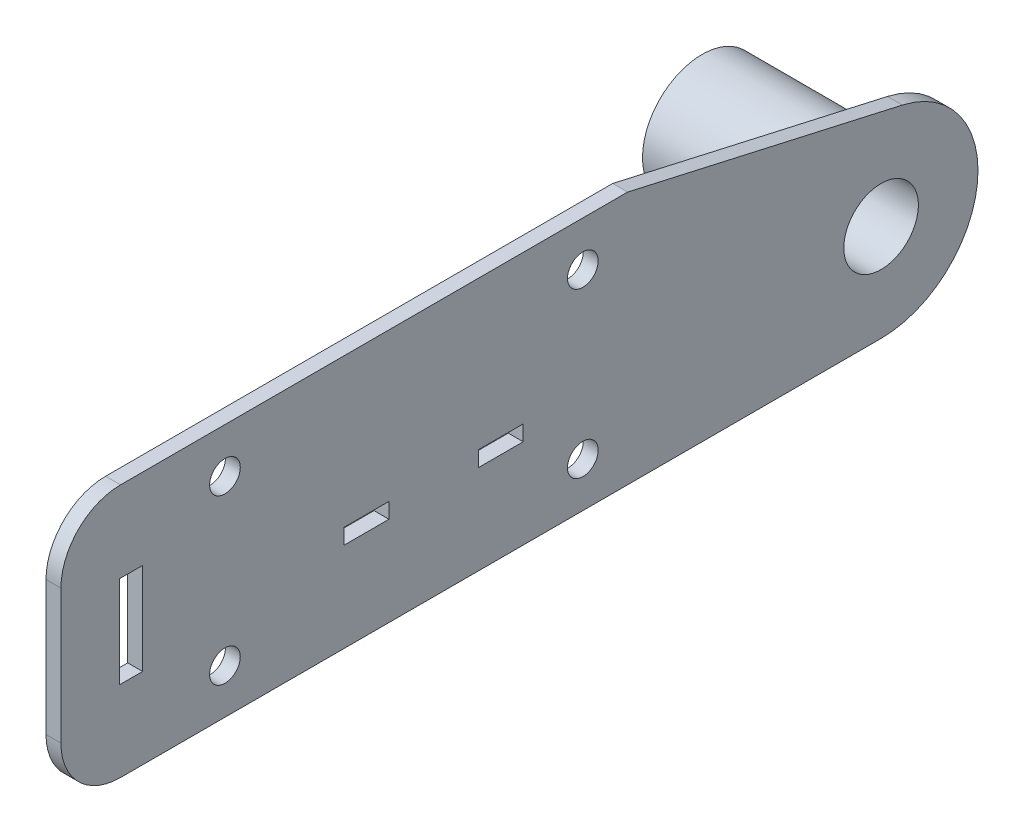
SolidWorks part; units mm, degrees
material "Plain Carbon Steel"
ref_plane "Front Plane" through (0, 0, 0) normal (0, 0, 1) x (1, 0, 0)
ref_plane "Top Plane" through (0, 0, 0) normal (0, 1, 0) x (1, 0, 0)
ref_plane "Right Plane" through (0, 0, 0) normal (1, 0, 0) x (0, 0, -1)
sketch "Sketch1" plane through (0, 0, 0) normal (1, 0, 0) x (0, 0, -1)
  line L0 (47.625, -26.9875) -> (101.6, -26.9875)
  line L1 (38.1, 17.4625) -> (-38.1, 17.4625)
  line L2 (38.1, 17.4625) -> (38.1, -17.4625)
  line L3 (38.1, -17.4625) -> (-38.1, -17.4625)
  line L4 (-38.1, 17.4625) -> (-38.1, -17.4625)
  line L5 (38.1, 17.4625) -> (-38.1, -17.4625) construction
  line L6 (38.1, -17.4625) -> (-38.1, 17.4625) construction
  line L7 (-47.625, 26.9875) -> (47.625, 26.9875)
  line L8 (-47.625, 26.9875) -> (-47.625, -26.9875)
  line L9 (-47.625, -26.9875) -> (47.625, -26.9875)
  line L10 (47.625, 26.9875) -> (47.625, -26.9875)
  line L11 (-47.625, 26.9875) -> (47.625, -26.9875) construction
  line L12 (-47.625, -26.9875) -> (47.625, 26.9875) construction
  line L13 (47.625, 26.9875) -> (106.1432, 13.7812)
  circle A0 centre (-38.1, 17.4625) radius 3.2639
  circle A1 centre (-38.1, -17.4625) radius 3.2639
  circle A2 centre (38.1, -17.4625) radius 3.2639
  circle A3 centre (38.1, 17.4625) radius 3.2639
  circle A4 centre (101.6, -6.35) radius 12.7
  circle A5 centre (101.6, -6.35) radius 20.6375
  point P0 (0, 0)
  point P13 (0, 0)
  dimension "D3" = 6.5278
  dimension "D4" = 25.4
  dimension "D1" = 76.2
  dimension "D2" = 34.925
  dimension "D5" = 63.5
  dimension "D6" = 6.35
  dimension "D8" = 9.525
  dimension "D9" = 9.525
extrude "Boss-Extrude1" add sketch "Sketch1" along normal blind 3.175 contours L10 L7 L8 L9 A3 L2 A2 L3 A1 L4 A0 L1 | A3 L1 A0 L4 A1 L3 A2 L2 | A5 L13 L10 L0 | A5 A4
sketch "Sketch2" plane through (0, 0, 0) normal (-1, 0, 0) x (0, 0, 1)
  circle A0 centre (-101.6, -6.35) radius 12.7 construction
  circle A1 centre (-101.6, -6.35) radius 12.7
  circle A2 centre (-101.6, -6.35) radius 7.9375
  dimension "D1" = 4.7625
extrude "Boss-Extrude2" add sketch "Sketch2" along normal blind 34.925 and the other way blind 3.175
sketch "Sketch4" plane through (3.175, 0, 0) normal (1, 0, 0) x (0, 0, -1)
  line L0 (-47.625, -26.9875) -> (101.6, -26.9875) construction
  line L1 (-47.625, 26.9875) -> (-60.325, 26.9875)
  line L2 (-47.625, 26.9875) -> (-47.625, -26.9875)
  line L3 (-47.625, -26.9875) -> (-60.325, -26.9875)
  line L4 (-73.025, 14.2875) -> (-73.025, -14.2875)
  line L6 (-60.579, 9.779) -> (-55.626, 9.779)
  line L7 (-60.579, 9.779) -> (-60.579, -9.779)
  line L8 (-60.579, -9.779) -> (-55.626, -9.779)
  line L9 (-55.626, 9.779) -> (-55.626, -9.779)
  arc A0 (-60.325, 26.9875) -> (-73.025, 14.2875) centre (-60.325, 14.2875) ccw
  arc A1 (-60.325, -26.9875) -> (-73.025, -14.2875) centre (-60.325, -14.2875) cw
  point P13 (-73.025, 26.9875)
  dimension "D6" = 12.7
  dimension "D1" = 25.4
  dimension "D2" = 19.558
  dimension "D3" = 4.953
  dimension "D4" = 17.2085
  dimension "D5" = 8.001
extrude "Boss-Extrude3" add sketch "Sketch4" against normal up to surface (3.175 mm away) up to face at (0, -17.4625, -41.3639)
sketch "Sketch5" plane through (3.175, 0, 0) normal (1, 0, 0) x (0, 0, -1)
  line L1 (15.875, -4.6355) -> (25.4, -4.6355)
  line L2 (15.875, -4.6355) -> (15.875, -7.9375)
  line L3 (15.875, -7.9375) -> (25.4, -7.9375)
  line L4 (25.4, -4.6355) -> (25.4, -7.9375)
  line L5 (-12.7, -4.6355) -> (-3.175, -4.6355)
  line L6 (-12.7, -4.6355) -> (-12.7, -7.9375)
  line L7 (-12.7, -7.9375) -> (-3.175, -7.9375)
  line L8 (-3.175, -4.6355) -> (-3.175, -7.9375)
  circle A0 centre (101.6, -6.35) radius 12.7 construction
  circle A1 centre (101.6, -6.35) radius 12.7 construction
  dimension "D1" = 3.302
  dimension "D2" = 1.5875
  dimension "D3" = 9.525
  dimension "D4" = 76.2
  dimension "D5" = 9.525
  dimension "D6" = 19.05
  dimension "D7" = 3.302
extrude "Cut-Extrude1" cut sketch "Sketch5" against normal through all
